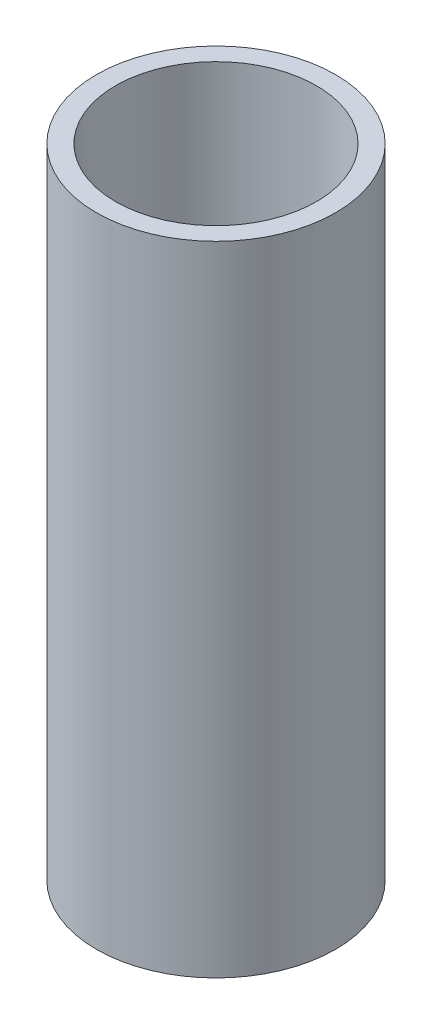
SolidWorks part; units mm, degrees
material "6061-T6 (SS)"
ref_plane "Front Plane" through (0, 0, 0) normal (0, 0, 1) x (1, 0, 0)
ref_plane "Top Plane" through (0, 0, 0) normal (0, 1, 0) x (1, 0, 0)
ref_plane "Right Plane" through (0, 0, 0) normal (1, 0, 0) x (0, 0, -1)
sketch "Sketch1" plane through (0, 0, 0) normal (0, 1, 0) x (1, 0, 0)
  circle A0 centre (0, 0) radius 9.525
  dimension "D1" = 19.05
extrude "Boss-Extrude1" add sketch "Sketch1" along normal blind 50.8
hole_wizard "Ø16.0 (16) Diameter Hole1" positions "Sketch2" profile "Sketch3" hole size "Ø16.0" standard "ANSI Metric"
sketch "Sketch2" plane through (0, 50.8, 0) normal (0, 1, 0) x (1, 0, 0)
  point P0 (0, 0)
sketch "Sketch3" plane through (0, 50.8, 0) normal (1, 0, 0) x (0, 0, 1)
  line L0 (0, 0) -> (0, 30.2069)
  line L1 (0, 30.2069) -> (8, 25.4)
  line L2 (8, 25.4) -> (8, 0)
  line L5 (8, 0) -> (0, 0)
  line L10 (0, 30.2069) -> (-8, 25.4) construction
  line L11 (0, -6.35) -> (0, 107.95) construction
  dimension "Hole Dia." = 16
  dimension "Hole Depth" = 25.4
  dimension "Drill Angle" = 118
hole_wizard "3/8 (0.375) Diameter Hole1" positions "Sketch4" profile "Sketch5" hole size "3/8" standard "ANSI Inch"
sketch "Sketch4" plane through (0, 0, 0) normal (0, -1, 0) x (-1, 0, 0)
  point P0 (0, 0)
sketch "Sketch5" plane through (0, 0, 0) normal (1, 0, 0) x (0, 0, -1)
  line L0 (0, 0) -> (0, 20.6416)
  line L1 (0, 20.6416) -> (4.7625, 17.78)
  line L2 (4.7625, 17.78) -> (4.7625, 0)
  line L5 (4.7625, 0) -> (0, 0)
  line L10 (0, 20.6416) -> (-4.7625, 17.78) construction
  line L11 (0, -6.35) -> (0, 107.95) construction
  dimension "Hole Dia." = 9.525
  dimension "Hole Depth" = 17.78
  dimension "Drill Angle" = 118
